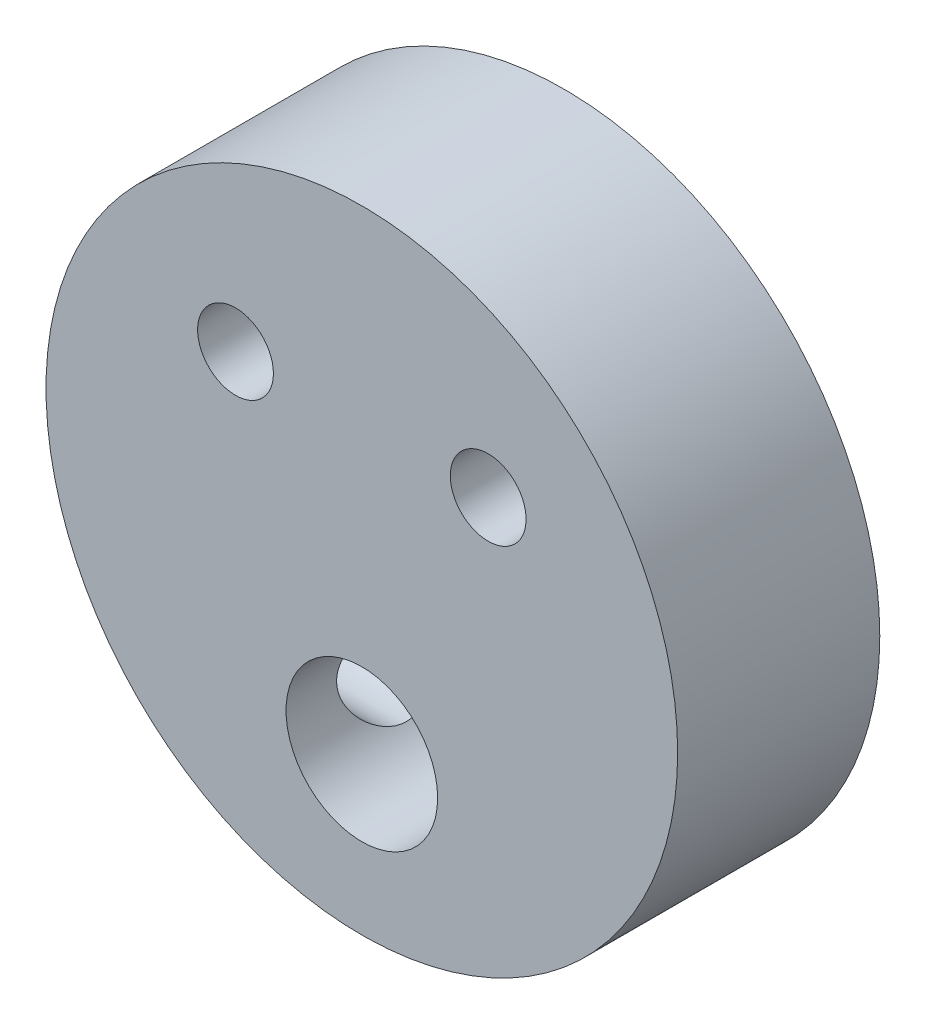
SolidWorks part; units mm, degrees
material "普通碳钢"
ref_plane "前视基准面" through (0, 0, 0) normal (0, 0, 1) x (1, 0, 0)
ref_plane "上视基准面" through (0, 0, 0) normal (0, 1, 0) x (1, 0, 0)
ref_plane "右视基准面" through (0, 0, 0) normal (1, 0, 0) x (0, 0, -1)
sketch "草图1" plane through (0, 0, 0) normal (0, 0, 1) x (1, 0, 0)
  line L0 (0, 12.5) -> (0, -12.5) construction
  line L1 (-12.5, 0) -> (12.5, 0) construction
  circle A0 centre (0, 0) radius 12.5
  circle A1 centre (0, -6.3) radius 3
  dimension "D1" = 25
  dimension "D2" = 6
  dimension "D3" = 6.3
extrude "凸台-拉伸1" add sketch "草图1" along normal blind 8
sketch "草图2" plane through (0, 0, 0) normal (1, 0, 0) x (0, 0, -1)
  line L0 (-8, -6.3) -> (0, -6.3) construction
  line L1 (-8, 12.5) -> (-8, -12.5) construction
  line L2 (0, -12.5) -> (0, 12.5) construction
  line L3 (0, -3.3) -> (-8, -3.3) construction
  line L4 (-8, -9.3) -> (0, -9.3) construction
  circle A0 centre (-4, -6.3) radius 2
  dimension "D1" = 4
extrude "切除-拉伸1" cut sketch "草图2" against normal through all
sketch "草图3" plane through (0, 0, 8) normal (0, 0, 1) x (1, 0, 0)
  line L0 (0, 0) -> (0, 12.5) construction
  line L1 (-11.4564, 5) -> (11.4564, 5) construction
  circle A0 centre (0, 0) radius 12.5 construction
  circle A1 centre (-5, 5) radius 1.5
  circle A2 centre (5, 5) radius 1.5
  dimension "D1" = 3
  dimension "D2" = 10
  dimension "D3" = 5
extrude "切除-拉伸2" cut sketch "草图3" against normal through all
